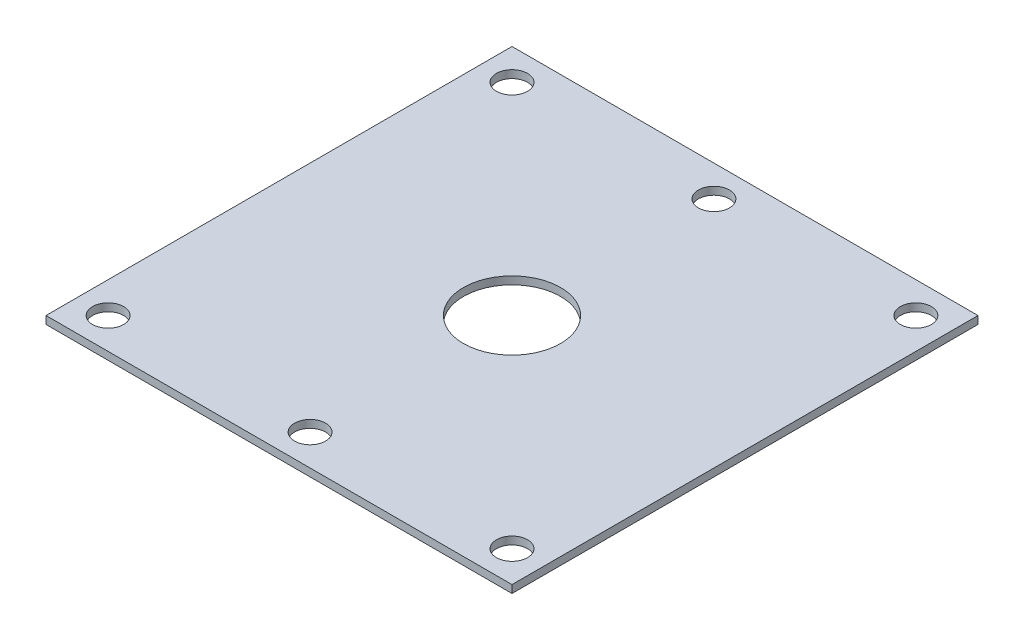
SolidWorks part; units mm, degrees
ref_plane "Front Plane" through (0, 0, 0) normal (0, 0, 1) x (1, 0, 0)
ref_plane "Top Plane" through (0, 0, 0) normal (0, 1, 0) x (1, 0, 0)
ref_plane "Right Plane" through (0, 0, 0) normal (1, 0, 0) x (0, 0, -1)
sketch "Sketch1" plane through (0, 0, 0) normal (0, 1, 0) x (1, 0, 0)
  line L1 (30, -30) -> (-30, -30)
  line L2 (30, -30) -> (30, 30)
  line L3 (30, 30) -> (-30, 30)
  line L4 (-30, -30) -> (-30, 30)
  line L5 (30, -30) -> (-30, 30) construction
  line L6 (30, 30) -> (-30, -30) construction
  point P0 (0, 0)
  dimension "D1" = 60
  dimension "D2" = 60
extrude "Boss-Extrude1" add sketch "Sketch1" along normal blind 1
sketch "Sketch2" plane through (0, 1, 0) normal (0, 1, 0) x (1, 0, 0)
  line L0 (30, 30) -> (-30, 30) construction
  line L2 (-30, 30) -> (-30, -30) construction
  line L3 (30, -30) -> (30, 30) construction
  line L5 (-30, -30) -> (30, -30) construction
  line L7 (-30, 30) -> (-30, -30) construction
  circle A0 centre (-26, 26) radius 2
  circle A1 centre (0, 26) radius 2
  circle A2 centre (26, 26) radius 2
  circle A3 centre (26, -26) radius 2
  circle A4 centre (0, -26) radius 2
  circle A5 centre (-26, -26) radius 2
  dimension "D1" = 4
  dimension "D5" = 4
  dimension "D7" = 4
  dimension "D10" = 4
  dimension "D16" = 4
  dimension "D17" = 4
  dimension "D2" = 4
  dimension "D3" = 4
  dimension "D4" = 4
  dimension "D6" = 0
  dimension "D8" = 4
  dimension "D9" = 4
  dimension "D11" = 4
  dimension "D12" = 4
  dimension "D13" = 4
  dimension "D14" = 4
  dimension "D15" = 4
  dimension "D18" = 0
extrude "Cut-Extrude1" cut sketch "Sketch2" against normal through all
sketch "Sketch4" plane through (0, 1, 0) normal (0, 1, 0) x (1, 0, 0)
  circle A0 centre (0, 0) radius 6.25
  dimension "D1" = 12.5
extrude "Cut-Extrude3" cut sketch "Sketch4" against normal blind 10
